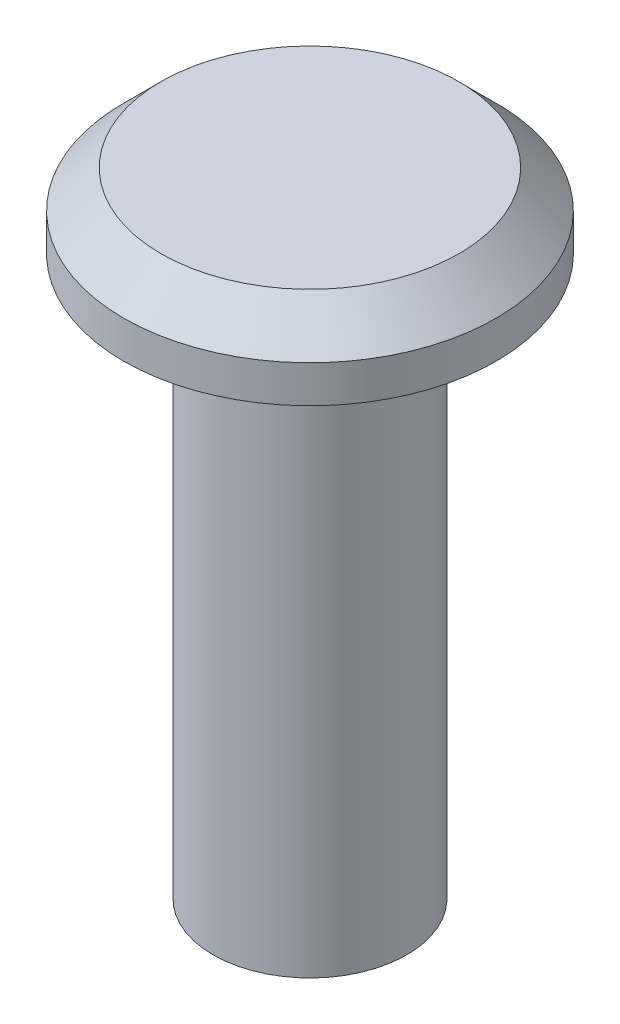
SolidWorks part; units mm, degrees
ref_plane "Front Plane" through (0, 0, 0) normal (0, 0, 1) x (1, 0, 0)
ref_plane "Top Plane" through (0, 0, 0) normal (0, 1, 0) x (1, 0, 0)
ref_plane "Right Plane" through (0, 0, 0) normal (1, 0, 0) x (0, 0, -1)
sketch "Sketch1" plane through (0, 0, 0) normal (0, 1, 0) x (1, 0, 0)
  circle A0 centre (0, 0) radius 2.6
  dimension "D1" = 5.2
extrude "Boss-Extrude1" add sketch "Sketch1" along normal blind 15
sketch "Sketch2" plane through (0, 15, 0) normal (0, 1, 0) x (1, 0, 0)
  circle A0 centre (0, 0) radius 5
  dimension "D1" = 10
extrude "Boss-Extrude2" add sketch "Sketch2" along normal blind 2
chamfer "Chamfer1" distance 1.2 angle 45 1 edges at (0, 15, 2.6)
chamfer "Chamfer2" distance 1 angle 45 1 edges at (0, 17, 5)
